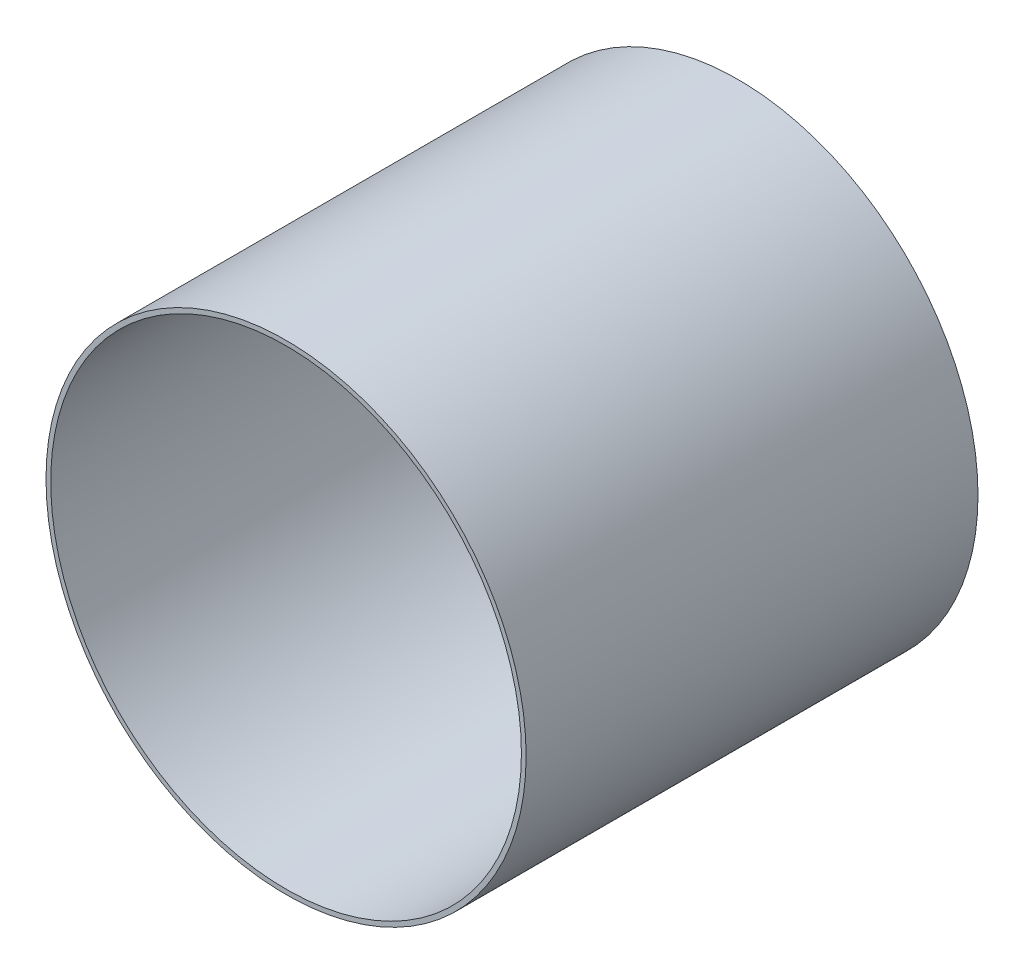
SolidWorks part; units mm, degrees
ref_plane "Front Plane" through (0, 0, 0) normal (0, 0, 1) x (1, 0, 0)
ref_plane "Top Plane" through (0, 0, 0) normal (0, 1, 0) x (1, 0, 0)
ref_plane "Right Plane" through (0, 0, 0) normal (1, 0, 0) x (0, 0, -1)
sketch "Sketch1" plane through (0, 0, 0) normal (0, 0, 1) x (1, 0, 0)
  circle A3 centre (0, 0) radius 25.5
  circle A4 centre (0, 0) radius 25
  circle A5 centre (0, 0) radius 25 construction
  dimension "D1" = 0.5
extrude "Boss-Extrude1" add sketch "Sketch1" against normal blind 48 contours A3 A4
